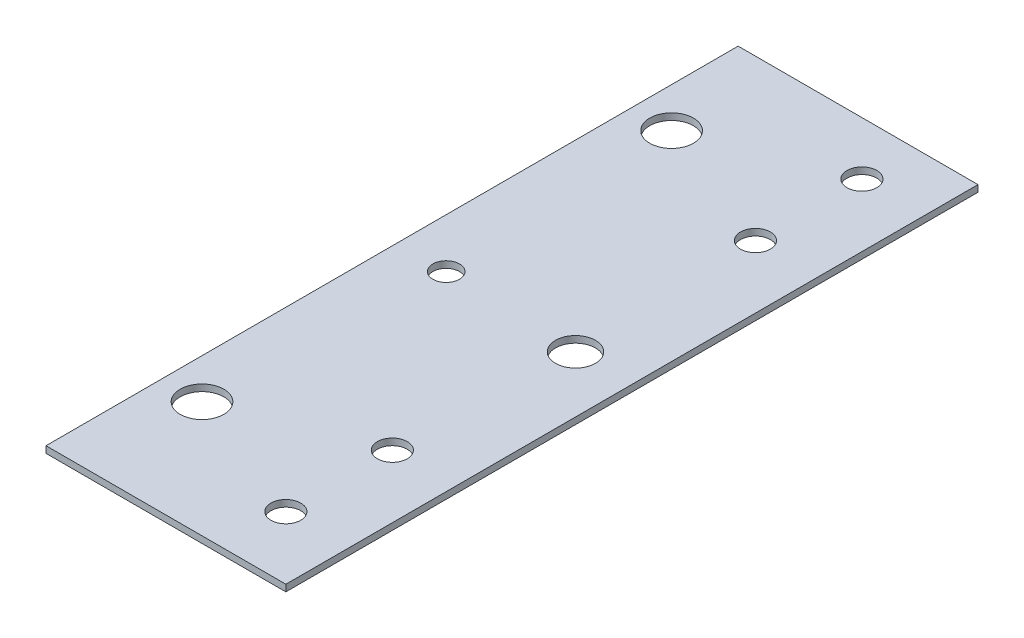
SolidWorks part; units mm, degrees
ref_plane "Front Plane" through (0, 0, 0) normal (0, 0, 1) x (1, 0, 0)
ref_plane "Top Plane" through (0, 0, 0) normal (0, 1, 0) x (1, 0, 0)
ref_plane "Right Plane" through (0, 0, 0) normal (1, 0, 0) x (0, 0, -1)
sketch "Sketch1" plane through (0, 0, 0) normal (0, 1, 0) x (1, 0, 0)
  line L0 (-19.0817, 56.007) -> (-19.0817, -56.007) construction
  line L1 (-28.6067, 81.407) -> (28.6068, 81.407)
  line L2 (-28.6067, 81.407) -> (-28.6067, -81.407)
  line L3 (-28.6067, -81.407) -> (28.6068, -81.407) construction
  line L4 (28.6068, 81.407) -> (28.6068, -81.407)
  line L5 (-28.6067, 81.407) -> (28.6068, -81.407) construction
  line L6 (-28.6067, -81.407) -> (28.6068, 81.407) construction
  line L7 (-19.0817, 0) -> (0, 0) construction
  line L8 (13.6208, -68.707) -> (13.6208, 68.707) construction
  line L9 (-19.0817, -56.007) -> (60.5742, -56.007) construction
  line L10 (-19.0817, 56.007) -> (37.012, 56.007) construction
  line L11 (-28.6067, -81.407) -> (-28.6067, -83.693)
  line L12 (-28.6067, -83.693) -> (28.6068, -83.693)
  line L13 (28.6068, -83.693) -> (28.6068, -81.407)
  circle A0 centre (-19.0817, 56.007) radius 5.207
  circle A1 centre (-19.0817, -56.007) radius 5.207
  circle A2 centre (13.6208, 68.707) radius 3.556
  circle A3 centre (13.6208, 43.307) radius 3.556
  circle A4 centre (13.6208, -43.307) radius 3.556
  circle A5 centre (13.6208, -68.707) radius 3.556
  point P0 (0, 0)
  dimension "D1" = 112.014
  dimension "D2" = 10.414
  dimension "D3" = 7.112
  dimension "D4" = 25.4
  dimension "D5" = 25.4
  dimension "D6" = 12.7
  dimension "D7" = 12.7
  dimension "D8" = 32.7025
  dimension "D9" = 14.986
  dimension "D10" = 9.525
  dimension "D11" = 12.7
  dimension "D12" = 165.1
extrude "Boss-Extrude1" add sketch "Sketch1" along normal blind 1.5875
sketch "Sketch2" plane through (0, 1.5875, 0) normal (0, 1, 0) x (1, 0, 0)
  circle A0 centre (-16.8498, 0.0106) radius 3.175
  dimension "D1" = 6.35
extrude "Cut-Extrude1" cut sketch "Sketch2" against normal through all
sketch "Sketch3" plane through (0, 1.5875, 0) normal (0, 1, 0) x (1, 0, 0)
  line L0 (28.6068, -83.693) -> (28.6068, 81.407) construction
  line L2 (28.6067, -1.143) -> (-28.6068, -1.143) construction
  line L3 (-28.6067, 81.407) -> (-28.6067, -83.693) construction
  circle A0 centre (15.1447, -1.143) radius 4.7625
  dimension "D1" = 43.7515
  dimension "D2" = 9.525
extrude "Cut-Extrude2" cut sketch "Sketch3" against normal blind 2.54
